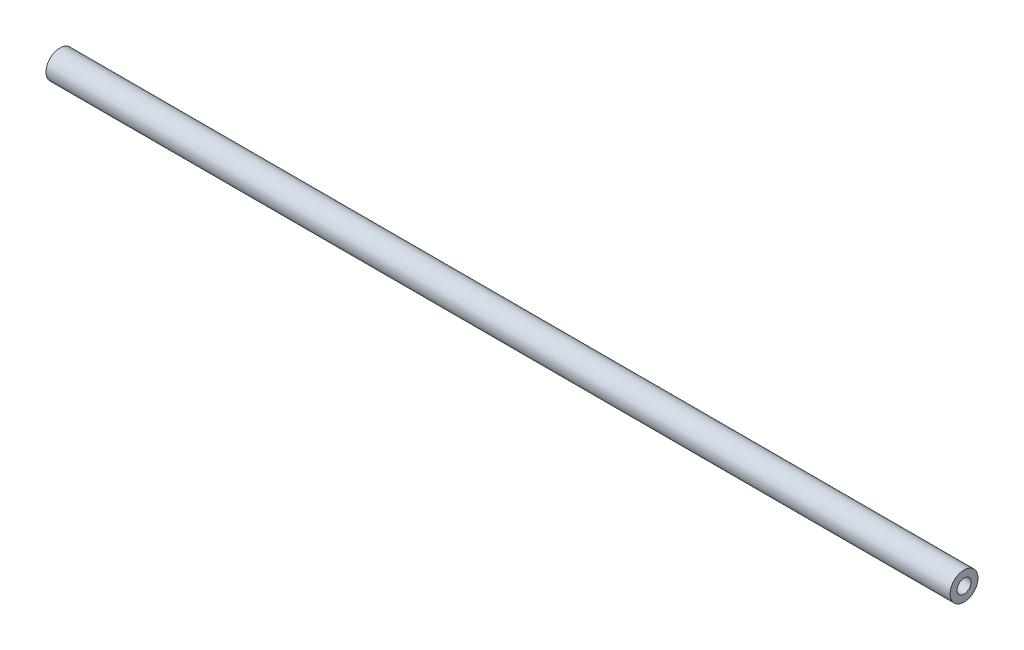
SolidWorks part; units mm, degrees
ref_plane "Front" through (0, 0, 0) normal (0, 0, 1) x (1, 0, 0)
ref_plane "Top" through (0, 0, 0) normal (0, 1, 0) x (1, 0, 0)
ref_plane "Right" through (0, 0, 0) normal (1, 0, 0) x (0, 0, -1)
sketch "草图1" plane through (0, 0, 0) normal (1, 0, 0) x (0, 0, -1)
  circle A0 centre (0, 0) radius 4
  circle A1 centre (0, 0) radius 2
  dimension "D1" = 8
  dimension "D2" = 4
extrude "凸台-拉伸1" add sketch "草图1" along normal up to vertex (247.54 mm away) and the other way up to vertex (12 mm away)
